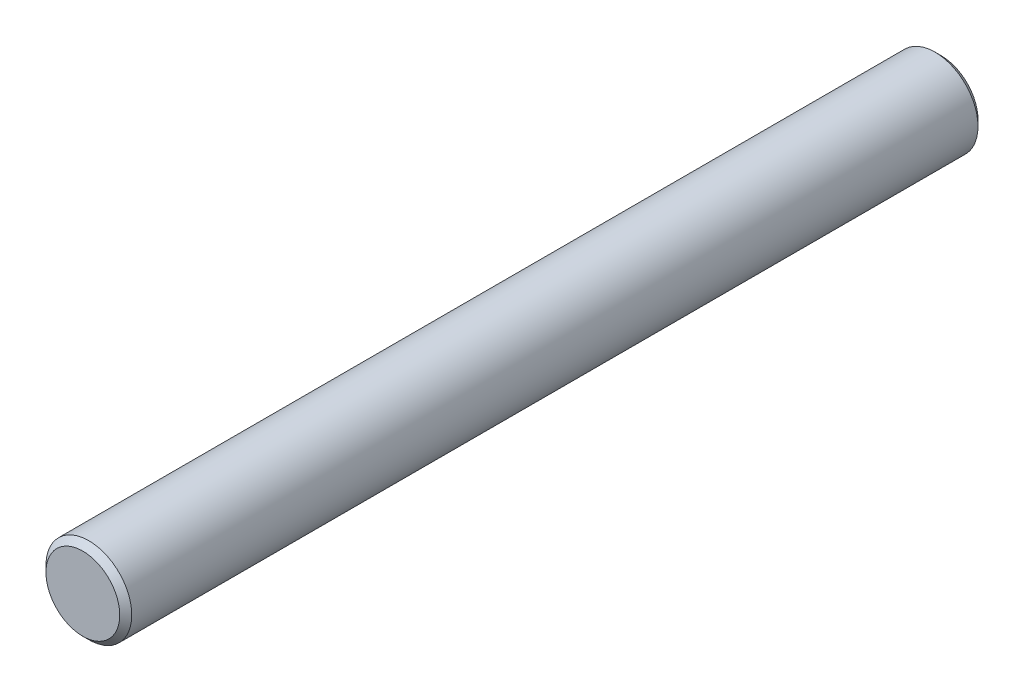
SolidWorks part; units mm, degrees
ref_plane "Front Plane" through (0, 0, 0) normal (0, 0, 1) x (1, 0, 0)
ref_plane "Top Plane" through (0, 0, 0) normal (0, 1, 0) x (1, 0, 0)
ref_plane "Right Plane" through (0, 0, 0) normal (1, 0, 0) x (0, 0, -1)
sketch "Sketch1" plane through (0, 0, 0) normal (0, 0, 1) x (1, 0, 0)
  line L0 (-2.5, 0) -> (2.5, 0) construction
  line L5 (0, 2.5) -> (0, -2.5) construction
  circle A1 centre (0, 0) radius 2.5
  point P7 (-2.5, 0)
  point P8 (2.5, 0)
  point P12 (0, -2.5)
  point P13 (0, 2.5)
  dimension "Diameter" = 5
sketch "Sketch2" plane through (0, 0, 0) normal (1, 0, 0) x (0, 0, -1)
  line L0 (-20, -2.5) -> (-20, 2.5) construction
  line L1 (25, -2.5) -> (-25, -2.5)
  line L2 (25, -2.5) -> (25, 2.5)
  line L3 (25, 2.5) -> (-25, 2.5)
  line L4 (-25, -2.5) -> (-25, 2.5)
  line L5 (25, -2.5) -> (-25, 2.5) construction
  line L6 (25, 2.5) -> (-25, -2.5) construction
  line L7 (20, -2.5) -> (20, 2.5) construction
  line L8 (-25, 2.15) -> (-24.65, 2.5) construction
  point P0 (0, 0)
  point P8 (-25, 2.5)
  point P9 (25, 2.5)
  point P14 (-20, 2.5)
  point P15 (-20, -2.5)
  point P16 (20, 2.5)
  point P17 (20, -2.5)
  point P25 (0, -2.5)
  dimension "Length" = 50
  dimension "D1" = 5
  dimension "D2" = 5
  dimension "Chamfer Typ," = 45
  dimension "D4" = 0.35
sketch "Sketch3" plane through (0, 0, 0) normal (0, 0, 1) x (1, 0, 0)
  circle A0 centre (0, 0) radius 2.5 construction
  circle A1 centre (0, 0) radius 2.5
extrude "Boss-Extrude1" add sketch "Sketch3" along normal up to vertex (25 mm away) and the other way up to vertex (25 mm away) up to point (0, 2.5, 25) other way up to point (0, 2.5, -25)
chamfer "Chamfer1" distance 0.35 angle 45 2 edges at (2.5, 0, -25) (2.5, 0, 25)
equation "\"D1@Sketch2\"=\"Diameter@Sketch1\""
equation "\"D2@Sketch2\"=\"Diameter@Sketch1\""
equation "\"D1@Chamfer1\"=\"Diameter@Sketch1\"*.07"
equation "\"D4@Sketch2\"=\"Diameter@Sketch1\"*.07"
equation "\"D2@Chamfer1\"=\"Chamfer Typ,@Sketch2\""
